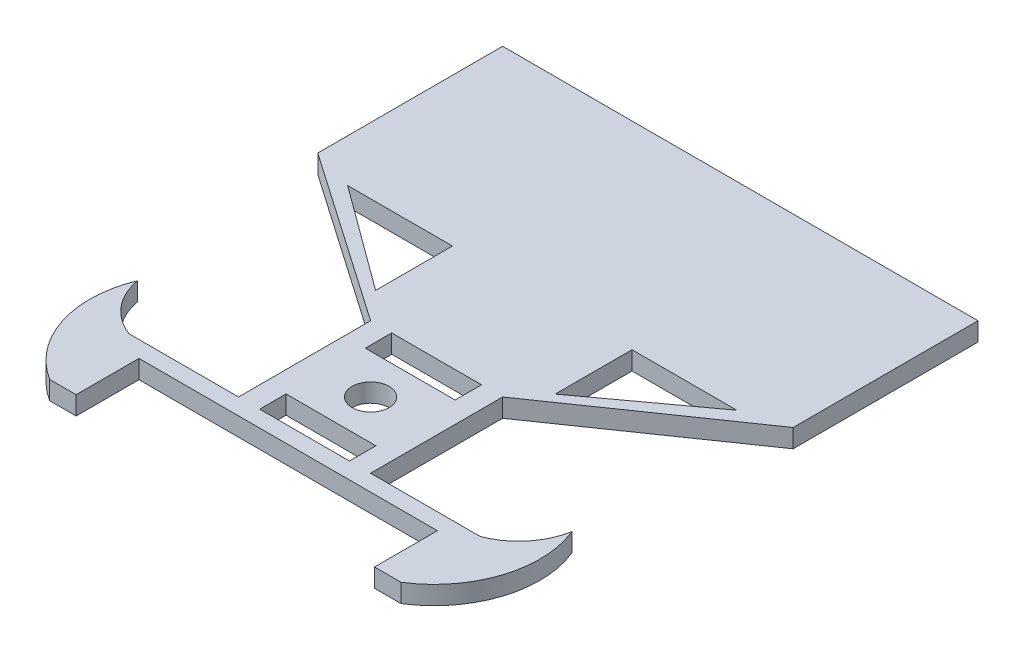
SolidWorks part; units mm, degrees
ref_plane "Front Plane" through (0, 0, 0) normal (0, 0, 1) x (1, 0, 0)
ref_plane "Top Plane" through (0, 0, 0) normal (0, 1, 0) x (1, 0, 0)
ref_plane "Right Plane" through (0, 0, 0) normal (1, 0, 0) x (0, 0, -1)
sketch "Sketch1" plane through (0, 0, 0) normal (0, 1, 0) x (1, 0, 0)
  line L0 (90, 0) -> (-90, 0)
  line L1 (-90, 0) -> (-90, -70)
  line L2 (-90, -70) -> (-25, -115)
  line L3 (-25, -115) -> (-25, -165)
  line L4 (-25, -165) -> (-66.5, -165)
  line L5 (-66.5, -165) -> (-66.5, -195)
  line L6 (-66.5, -195) -> (66.5, -195)
  line L7 (0, -55) -> (0, 55) construction
  line L8 (90, 0) -> (90, -70)
  line L9 (90, -70) -> (25, -115)
  line L10 (25, -165) -> (66.5, -165)
  line L11 (25, -115) -> (25, -165)
  line L12 (66.5, -165) -> (66.5, -195)
  point P12 (0, 0)
  point P17 (0, -195)
  dimension "D1" = 180
  dimension "D2" = 70
  dimension "D3" = 50
  dimension "D4" = 50
  dimension "D5" = 30
  dimension "D6" = 133
  dimension "D7" = 195
extrude "Boss-Extrude1" add sketch "Sketch1" along normal mid plane 7
sketch "Sketch2" plane through (0, 3.5, 0) normal (0, 1, 0) x (1, 0, 0)
  line L0 (-66.5, -165) -> (-66.5, -195)
  line L1 (0, -55) -> (0, 55) construction
  line L2 (66.5, -165) -> (66.5, -195)
  arc A0 (-66.5, -165) -> (-82.2688, -146.0433) centre (-57.6644, -141.6134) cw
  arc A1 (-66.5, -195) -> (-82.2688, -146.0433) centre (-45.2225, -161.1287) cw
  arc A2 (66.5, -195) -> (82.2688, -146.0433) centre (45.2225, -161.1287) ccw
  arc A3 (66.5, -165) -> (82.2688, -146.0433) centre (57.6644, -141.6134) ccw
  dimension "D1" = 40
  dimension "D2" = 25
extrude "Boss-Extrude2" add sketch "Sketch2" against normal blind 7
sketch "Sketch3" plane through (0, 3.5, 0) normal (0, 1, 0) x (1, 0, 0)
  line L0 (90, 0) -> (-90, 0) construction
  line L1 (-61.6286, -10) -> (-1.6286, -10)
  line L2 (-61.6286, -10) -> (-61.6286, -40)
  line L3 (-61.6286, -40) -> (-1.6286, -40)
  line L4 (-1.6286, -10) -> (-1.6286, -40)
  line L5 (-61.6286, -10) -> (-1.6286, -40) construction
  line L6 (-61.6286, -40) -> (-1.6286, -10) construction
  line L7 (8.3714, -10) -> (68.3714, -10)
  line L8 (8.3714, -10) -> (8.3714, -65)
  line L9 (8.3714, -65) -> (68.3714, -65)
  line L10 (68.3714, -10) -> (68.3714, -65)
  line L11 (8.3714, -10) -> (68.3714, -65) construction
  line L12 (8.3714, -65) -> (68.3714, -10) construction
  line L13 (-49.3397, -47) -> (-5.3397, -47)
  line L14 (-49.3397, -47) -> (-49.3397, -65)
  line L15 (-49.3397, -65) -> (-5.3397, -65)
  line L16 (-5.3397, -47) -> (-5.3397, -65)
  line L17 (-49.3397, -47) -> (-5.3397, -65) construction
  line L18 (-49.3397, -65) -> (-5.3397, -47) construction
  line L19 (-86.3397, -50) -> (-59.3397, -50)
  line L20 (-86.3397, -50) -> (-86.3397, -62.7)
  line L21 (-86.3397, -62.7) -> (-59.3397, -62.7)
  line L22 (-59.3397, -50) -> (-59.3397, -62.7)
  line L23 (-86.3397, -50) -> (-59.3397, -62.7) construction
  line L24 (-86.3397, -62.7) -> (-59.3397, -50) construction
  line L25 (-24, -75) -> (24, -75)
  line L26 (-24, -75) -> (-24, -110)
  line L27 (-24, -110) -> (24, -110)
  line L28 (24, -75) -> (24, -110)
  line L29 (-24, -75) -> (24, -110) construction
  line L30 (-24, -110) -> (24, -75) construction
  point P0 (-31.6286, -25)
  point P5 (38.3714, -37.5)
  point P10 (-27.3397, -56)
  point P15 (-72.8397, -56.35)
  point P20 (0, -92.5)
  point P25 (46.8434, -58.4613)
  point P26 (45.6767, -64.8465)
  point P27 (148.4528, -45.189)
  point P28 (98.0459, -104.2381)
  point P29 (144.033, -94.9582)
  point P30 (-122.6095, -16.3884)
  point P31 (-56.0005, 29.5987)
  point P32 (38.3714, -37.4012)
  point P33 (-40.4819, -23.9533)
  point P34 (-27.3397, -62.689)
  point P35 (-67.3776, -62.1574)
  point P36 (0, -93.332)
  dimension "D1" = 44
  dimension "D2" = 18
  dimension "D3" = 60
  dimension "D4" = 55
  dimension "D5" = 30
  dimension "D6" = 60
  dimension "D7" = 27
  dimension "D8" = 12.7
  dimension "D9" = 48
  dimension "D10" = 35
  dimension "D11" = 10
  dimension "D12" = 10
  dimension "D13" = 10
  dimension "D14" = 10
  dimension "D15" = 10
  dimension "D16" = 10
  dimension "D17" = 10
sketch "Sketch6" plane through (0, 3.5, 0) normal (0, 1, 0) x (1, 0, 0)
  line L0 (-25, -115) -> (25, -115)
  line L1 (-25, -155) -> (25, -155)
  line L2 (-25, -155) -> (-25, -125)
  line L3 (-25, -125) -> (25, -125)
  line L4 (25, -155) -> (25, -125)
  line L5 (-25, -155) -> (25, -125) construction
  line L6 (-25, -125) -> (25, -155) construction
  line L7 (-25, -165) -> (25, -165)
  line L8 (25, -165) -> (25, -115) construction
  line L9 (-17, -125) -> (-17, -115)
  line L10 (17, -115) -> (17, -125)
  line L11 (-17, -155) -> (-17, -165)
  line L12 (17, -155) -> (17, -165)
  line L13 (-25, -115) -> (-25, -165) construction
  line L14 (-25, -125) -> (-25, -115)
  line L15 (-17, -125) -> (-25, -125)
  line L16 (-25, -115) -> (-17, -115)
  line L17 (-25, -165) -> (-17, -165)
  line L18 (-25, -165) -> (-25, -155)
  line L19 (-17, -155) -> (-25, -155)
  line L20 (17, -155) -> (25, -155)
  line L21 (25, -165) -> (25, -155)
  line L22 (17, -165) -> (25, -165)
  line L23 (-17, -125) -> (17, -125)
  line L24 (-17, -115) -> (17, -115)
  line L25 (-17, -165) -> (17, -165)
  line L26 (-17, -155) -> (17, -155)
  point P0 (0, -140)
  dimension "D1" = 50
  dimension "D2" = 30
  dimension "D3" = 8
  dimension "D4" = 8
extrude "Cut-Extrude1" cut sketch "Sketch6" against normal blind 7 contours L12 L1 L11 L7 | L10 L0 L9 L3
sketch "Sketch7" plane through (0, 3.5, 0) normal (0, 1, 0) x (1, 0, 0)
  circle A1 centre (0, -140) radius 7
  dimension "D2" = 14
extrude "Cut-Extrude2" cut sketch "Sketch7" against normal blind 7
sketch "Sketch8" plane through (0, 3.5, 0) normal (0, 1, 0) x (1, 0, 0)
  circle A0 centre (0, -140) radius 14
  dimension "D1" = 28
sketch "Sketch9" plane through (0, 3.5, 0) normal (0, 1, 0) x (1, 0, 0)
  line L0 (-34, -75) -> (-73.6959, -75)
  line L1 (-73.6959, -75) -> (-34, -104.0977)
  line L2 (-34, -104.0977) -> (-34, -75)
  line L4 (-49.3397, -65) -> (-5.3397, -65) construction
  line L8 (0, -55) -> (0, 55) construction
  line L9 (34, -104.0977) -> (34, -75)
  line L10 (73.6959, -75) -> (34, -104.0977)
  line L11 (34, -75) -> (73.6959, -75)
  dimension "D1" = 10
extrude "Cut-Extrude3" cut sketch "Sketch9" against normal blind 7
sketch "Sketch11" plane through (0, 3.5, 0) normal (0, 1, 0) x (1, 0, 0)
  line L0 (-66.5, -195) -> (66.5, -195) construction
  line L1 (-56.5, -195) -> (56.5, -195)
  line L2 (-56.5, -195) -> (-56.5, -171.2)
  line L3 (-56.5, -171.2) -> (56.5, -171.2)
  line L4 (56.5, -171.2) -> (56.5, -195)
  point P5 (0, -195)
  dimension "D1" = 113
  dimension "D2" = 23.8
extrude "Cut-Extrude4" cut sketch "Sketch11" against normal blind 7
